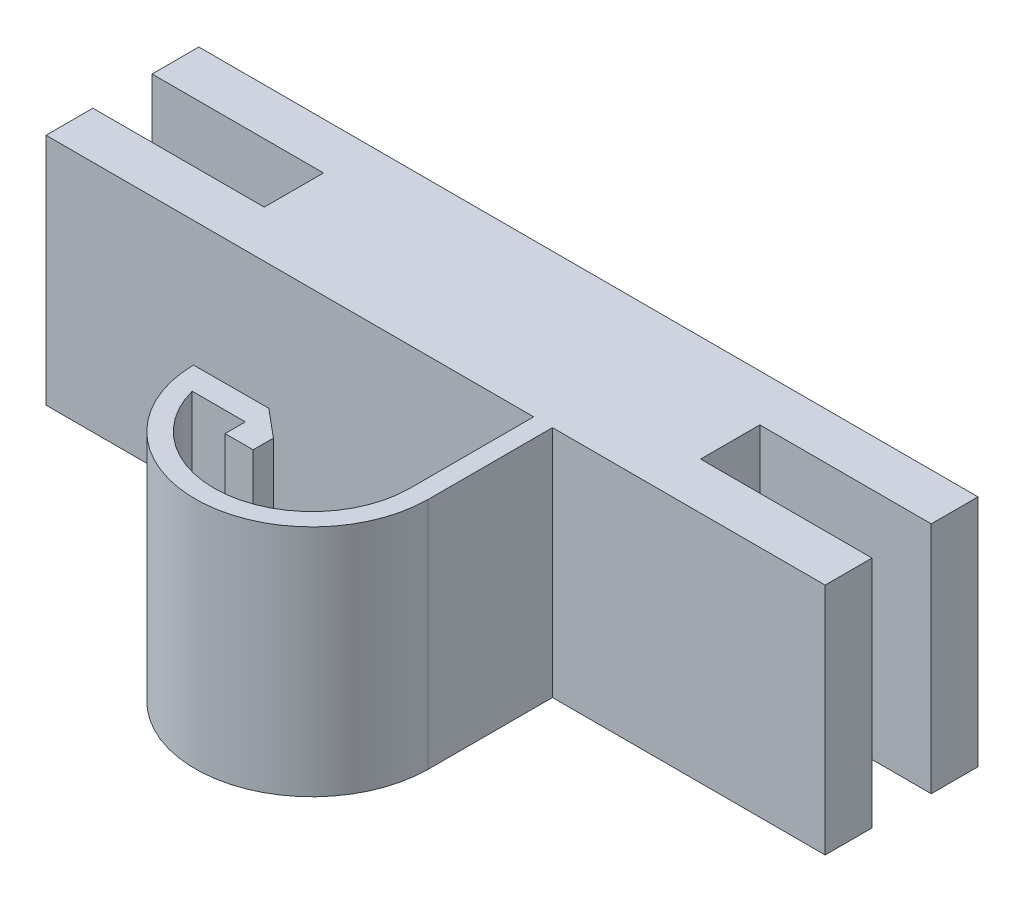
SolidWorks part; units mm, degrees
ref_plane "Front Plane" through (0, 0, 0) normal (0, 0, 1) x (1, 0, 0)
ref_plane "Top Plane" through (0, 0, 0) normal (0, 1, 0) x (1, 0, 0)
ref_plane "Right Plane" through (0, 0, 0) normal (1, 0, 0) x (0, 0, -1)
sketch "Sketch2" plane through (0, 0, 0) normal (0, 1, 0) x (1, 0, 0)
  line L0 (-28.3495, 21.9641) -> (-17.3495, 21.9641)
  line L1 (-28.3495, 28.7641) -> (21.6505, 28.7641)
  line L2 (-28.3495, 28.7641) -> (-28.3495, 25.7641)
  line L3 (-28.3495, 25.7641) -> (-17.3495, 25.7641)
  line L4 (21.6505, 28.7641) -> (21.6505, 25.7641)
  line L5 (-28.3495, 21.9641) -> (-28.3495, 18.957)
  line L6 (-28.3495, 18.957) -> (2.9478, 18.957)
  line L7 (21.6505, 21.9641) -> (21.6505, 18.957)
  line L8 (-17.3495, 25.7641) -> (-17.3495, 21.9641)
  line L9 (10.6505, 25.7641) -> (10.6505, 21.9641)
  line L10 (10.6505, 21.9641) -> (21.6505, 21.9641)
  line L11 (10.6505, 25.7641) -> (21.6505, 25.7641)
  line L12 (-10.8477, 10.9173) -> (-6.0262, 10.9324)
  line L13 (-6.0262, 10.9324) -> (-4.2225, 9.4232)
  line L14 (4.1505, 18.957) -> (4.1505, 10.957)
  line L15 (-4.2225, 9.4232) -> (-4.2225, 8.1222)
  line L16 (-4.2225, 8.1222) -> (-6.026, 8.1222)
  line L17 (2.9478, 10.957) -> (2.9478, 18.957)
  line L18 (4.1505, 18.957) -> (21.6505, 18.957)
  line L19 (-6.026, 8.1222) -> (-6.026, 9.4233)
  line L20 (-6.026, 9.4233) -> (-9.4377, 9.4233)
  arc A0 (-10.8477, 10.9173) -> (4.1505, 10.957) centre (-3.3488, 11.0292) ccw
  arc A1 (-9.4377, 9.4233) -> (2.9478, 10.957) centre (-3.3488, 11.0292) ccw
  dimension "D1" = 50
  dimension "D2" = 3
  dimension "D3" = 3.8
  dimension "D4" = 28
  dimension "D5" = 11
extrude "Boss-Extrude2" add sketch "Sketch2" along normal blind 15
